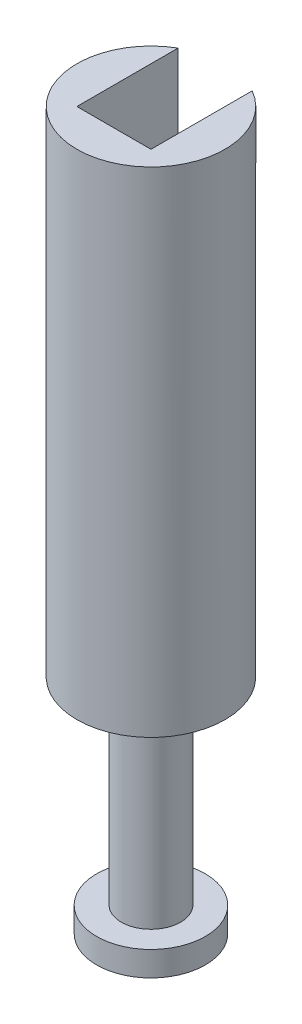
SolidWorks part; units mm, degrees
ref_plane "Front Plane" through (0, 0, 0) normal (0, 0, 1) x (1, 0, 0)
ref_plane "Top Plane" through (0, 0, 0) normal (0, 1, 0) x (1, 0, 0)
ref_plane "Right Plane" through (0, 0, 0) normal (1, 0, 0) x (0, 0, -1)
sketch "Sketch1" plane through (0, 0, 0) normal (0, 1, 0) x (1, 0, 0)
  circle A0 centre (0, 0) radius 15
  dimension "D1" = 30
extrude "Boss-Extrude1" add sketch "Sketch1" along normal blind 100
sketch "Sketch2" plane through (0, 0, 0) normal (0, -1, 0) x (1, 0, 0)
  circle A0 centre (0, 0) radius 6
  dimension "D1" = 12
sketch "Sketch3" plane through (0, 100, 0) normal (0, 1, 0) x (1, 0, 0)
  line L1 (-7.5, -7.5) -> (7.5, -7.5)
  line L2 (-7.5, -7.5) -> (-7.5, 7.5)
  line L3 (-7.5, 7.5) -> (7.5, 7.5)
  line L4 (7.5, -7.5) -> (7.5, 7.5)
  line L5 (-7.5, -7.5) -> (7.5, 7.5) construction
  line L6 (-7.5, 7.5) -> (7.5, -7.5) construction
  line L7 (-7.5, 7.5) -> (7.5, 7.5)
  line L8 (-7.5, 7.5) -> (-7.5, 15)
  line L9 (-7.5, 15) -> (7.5, 15)
  line L10 (7.5, 7.5) -> (7.5, 15)
  circle A0 centre (0, 0) radius 15 construction
  point P0 (0, 0)
  point P8 (7.5, 7.5)
  circle M5 centre (0, 0) radius 15
  dimension "D1" = 15
extrude "Cut-Extrude2" cut sketch "Sketch3" against normal blind 75 contours L1 L4 L3 L2 | L3 L10 L8 M5
extrude "Boss-Extrude2" add sketch "Sketch2" along normal blind 40
sketch "Sketch4" plane through (0, -40, 0) normal (0, -1, 0) x (-1, 0, 0)
  circle A0 centre (0, 0) radius 11
  dimension "D1" = 22
extrude "Boss-Extrude3" add sketch "Sketch4" along normal blind 5
